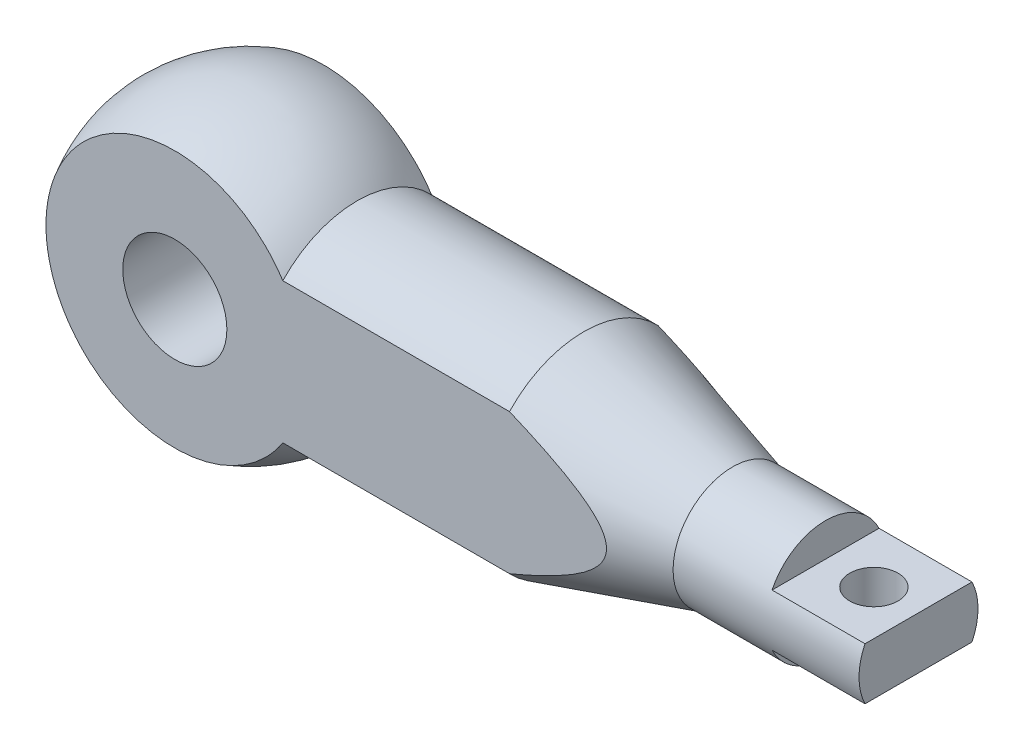
SolidWorks part; units mm, degrees
ref_plane "前基準面" through (0, 0, 0) normal (0, 0, 1) x (1, 0, 0)
ref_plane "上基準面" through (0, 0, 0) normal (0, 1, 0) x (1, 0, 0)
ref_plane "右基準面" through (0, 0, 0) normal (1, 0, 0) x (0, 0, -1)
sketch "草圖1" plane through (0, 0, 0) normal (0, 0, 1) x (1, 0, 0)
  line L0 (-119.8078, 0) -> (182.5119, 0) construction
  line L1 (29.0474, 27.5) -> (90, 27.5)
  line L2 (90, 27.5) -> (130, 16)
  line L3 (130, 16) -> (180, 16)
  line L4 (180, 16) -> (180, 0)
  line L5 (-40, 0) -> (180, 0)
  arc A0 (29.0474, 27.5) -> (-40, 0) centre (0, 0) ccw
  dimension "D1" = 40
  dimension "D5" = 180
  dimension "D6" = 130
  dimension "D2" = 55
  dimension "D3" = 32
  dimension "D4" = 40
revolve "旋轉1" add sketch "草圖1" angle 360 about L0
sketch "草圖3" plane through (0, 0, 0) normal (0, 1, 0) x (1, 0, 0)
  line L0 (-48.6165, 0) -> (115.3269, 0) construction
  line L1 (-40, -20) -> (180, -20)
  line L2 (-40, -20) -> (-40, 20)
  line L3 (-40, 20) -> (180, 20)
  line L4 (180, -20) -> (180, 20)
  line L6 (180, -16) -> (180, 16) construction
  arc A0 (29.0474, 27.5) -> (29.0474, -27.5) centre (0, 0) ccw construction
  dimension "D1" = 40
extrude "除料-伸長1" cut sketch "草圖3" against normal through all both and the other way through all flip side to cut
sketch "草圖4" plane through (0, 0, 20) normal (0, 0, 1) x (1, 0, 0)
  line L0 (180, -16) -> (180, 16) construction
  line L1 (180, 16) -> (155, 16)
  line L2 (180, 16) -> (180, 7)
  line L3 (180, 7) -> (155, 7)
  line L4 (155, 16) -> (155, 7)
  line L5 (0, 0) -> (192.9059, 0) construction
  line L6 (155, -16) -> (155, -7)
  line L7 (180, -7) -> (155, -7)
  line L8 (180, -16) -> (180, -7)
  line L9 (180, -16) -> (155, -16)
  circle A0 centre (0, 0) radius 14
  dimension "D1" = 28
  dimension "D2" = 25
  dimension "D3" = 7
  dimension "D4" = 16
extrude "除料-伸長2" cut sketch "草圖4" against normal through all
sketch "草圖5" plane through (0, 7, 0) normal (0, 1, 0) x (1, 0, 0)
  line L0 (180, 14.3875) -> (180, -14.3875) construction
  circle A0 centre (168, 0) radius 6.5
  dimension "D1" = 13
  dimension "D2" = 12
extrude "除料-伸長3" cut sketch "草圖5" against normal through all
